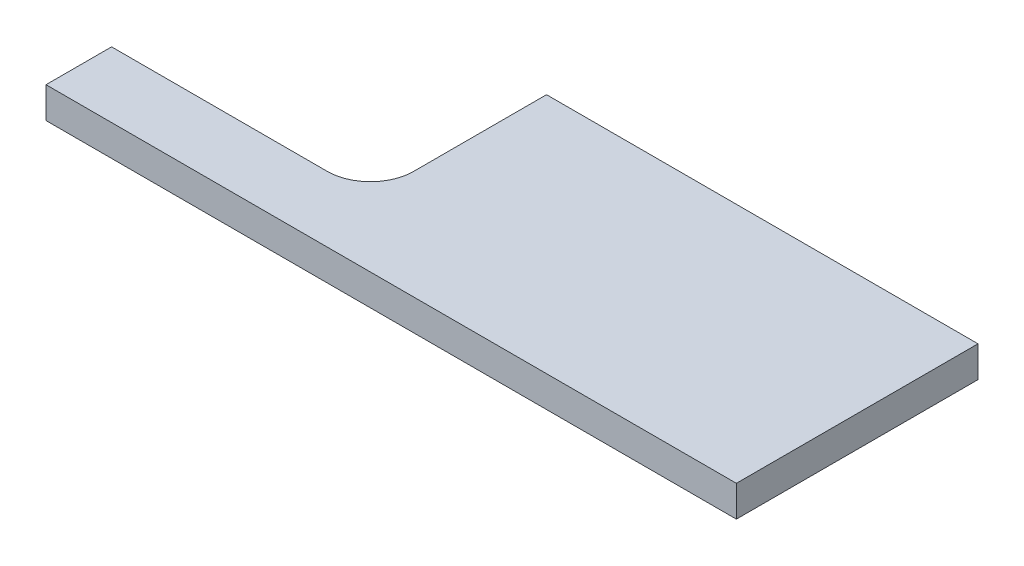
SolidWorks part; units mm, degrees
ref_plane "Front Plane" through (0, 0, 0) normal (0, 0, 1) x (1, 0, 0)
ref_plane "Top Plane" through (0, 0, 0) normal (0, 1, 0) x (1, 0, 0)
ref_plane "Right Plane" through (0, 0, 0) normal (1, 0, 0) x (0, 0, -1)
sketch "Sketch1" plane through (0, 0, 0) normal (0, 1, 0) x (1, 0, 0)
  line L0 (66.9815, 102) -> (316.9815, 102)
  line L1 (316.9815, 102) -> (316.9815, -38)
  line L2 (316.9815, -38) -> (-83.0185, -38)
  line L3 (-83.0185, -38) -> (-83.0185, 0)
  line L4 (-83.0185, 0) -> (41.9815, 0)
  line L5 (66.9815, 25) -> (66.9815, 102)
  arc A0 (41.9815, 0) -> (66.9815, 25) centre (41.9815, 25) ccw
  dimension "D4" = 25
  dimension "D1" = 250
  dimension "D2" = 140
  dimension "D3" = 38
  dimension "D5" = 77
  dimension "D6" = 400
extrude "Boss-Extrude1" add sketch "Sketch1" along normal blind 18
